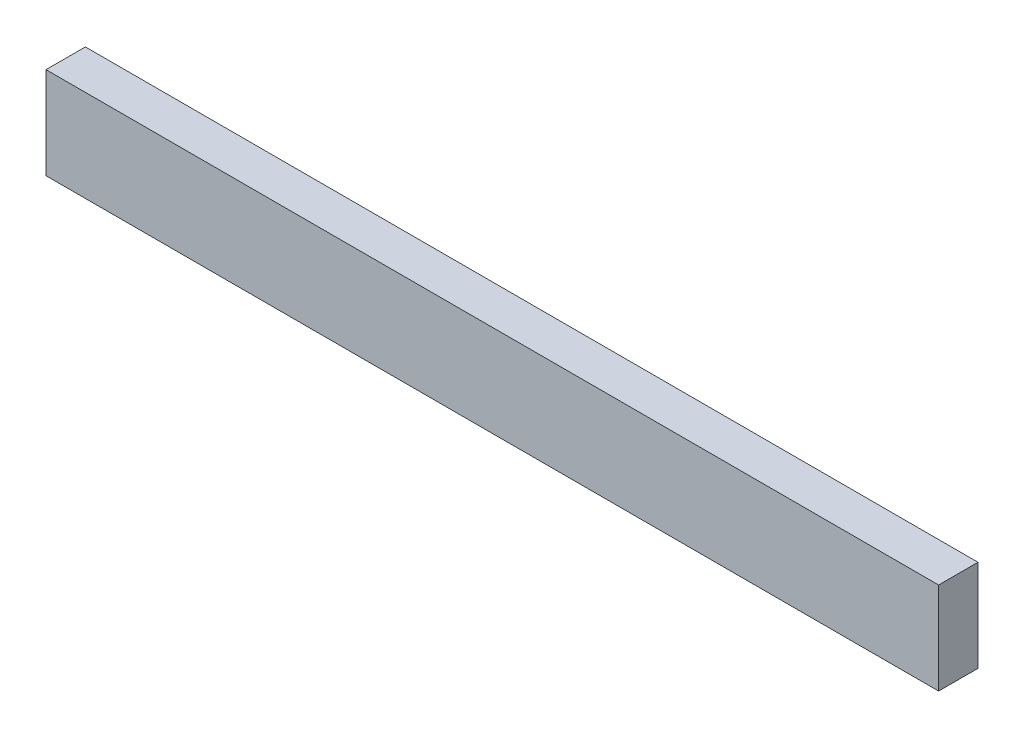
SolidWorks part; units mm, degrees
material "Cedar"
ref_plane "Front Plane" through (0, 0, 0) normal (0, 0, 1) x (1, 0, 0)
ref_plane "Top Plane" through (0, 0, 0) normal (0, 1, 0) x (1, 0, 0)
ref_plane "Right Plane" through (0, 0, 0) normal (1, 0, 0) x (0, 0, -1)
sketch "Sketch3" plane through (0, 0, 0) normal (1, 0, 0) x (0, 0, -1)
  line L1 (-19.05, -44.45) -> (19.05, -44.45)
  line L2 (-19.05, -44.45) -> (-19.05, 44.45)
  line L3 (-19.05, 44.45) -> (19.05, 44.45)
  line L4 (19.05, -44.45) -> (19.05, 44.45)
  line L5 (-19.05, -44.45) -> (19.05, 44.45) construction
  line L6 (-19.05, 44.45) -> (19.05, -44.45) construction
  point P0 (0, 0)
  dimension "D1" = 38.1
  dimension "D2" = 88.9
extrude "Boss-Extrude1" add sketch "Sketch3" along normal blind 431.8 and the other way blind 431.8
